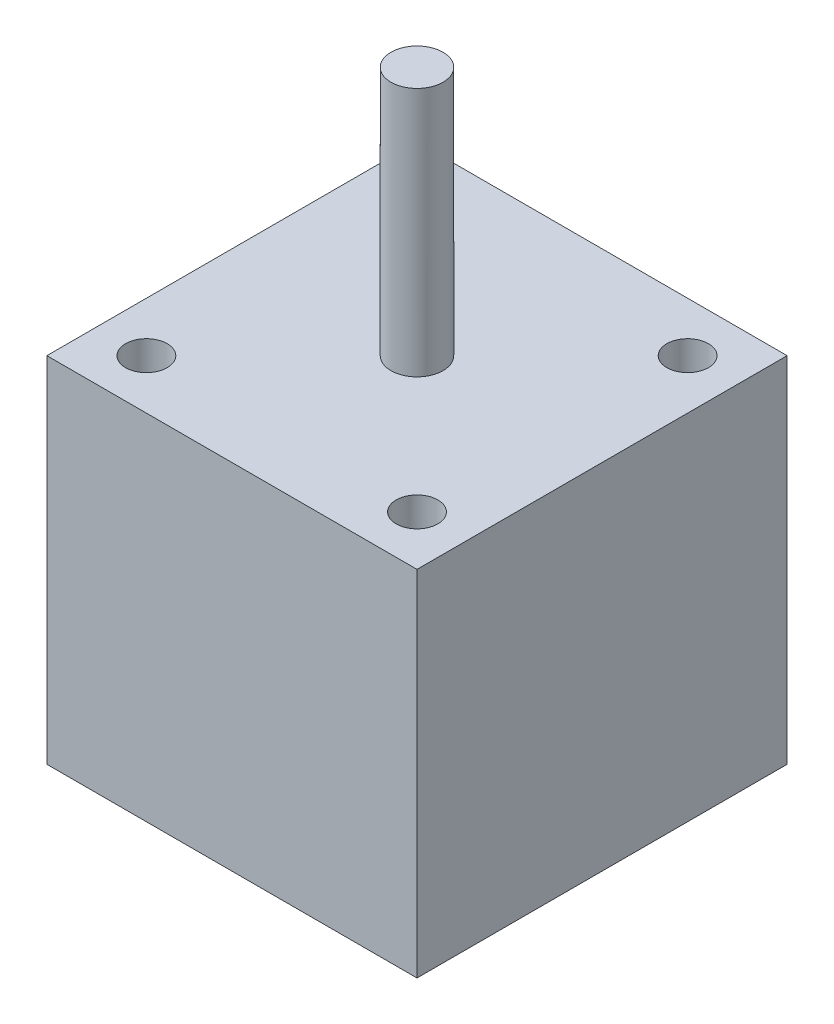
SolidWorks part; units mm, degrees
ref_plane "Front Plane" through (0, 0, 0) normal (0, 0, 1) x (1, 0, 0)
ref_plane "Top Plane" through (0, 0, 0) normal (0, 1, 0) x (1, 0, 0)
ref_plane "Right Plane" through (0, 0, 0) normal (1, 0, 0) x (0, 0, -1)
sketch "Sketch1" plane through (0, 0, 0) normal (0, 1, 0) x (1, 0, 0)
  line L1 (-17.78, -17.78) -> (17.78, -17.78)
  line L2 (-17.78, -17.78) -> (-17.78, 17.78)
  line L3 (-17.78, 17.78) -> (17.78, 17.78)
  line L4 (17.78, -17.78) -> (17.78, 17.78)
  line L5 (-17.78, -17.78) -> (17.78, 17.78) construction
  line L6 (-17.78, 17.78) -> (17.78, -17.78) construction
  point P0 (0, 0)
  dimension "D1" = 35.56
extrude "Boss-Extrude1" add sketch "Sketch1" along normal blind 34
sketch "Sketch2" plane through (0, 34, 0) normal (0, 1, 0) x (1, 0, 0)
  circle A0 centre (0, 0) radius 2.5
  dimension "D1" = 5
extrude "Boss-Extrude2" add sketch "Sketch2" along normal blind 24
sketch "Sketch3" plane through (0, 0, 0) normal (0, -1, 0) x (1, 0, 0)
  circle A0 centre (0, 0) radius 2.5
  dimension "D1" = 5
extrude "Boss-Extrude3" add sketch "Sketch3" along normal blind 12
sketch "Sketch4" plane through (0, 34, 0) normal (0, 1, 0) x (1, 0, 0)
  line L1 (-13, 13) -> (13, 13) construction
  line L2 (-13, 13) -> (-13, -13) construction
  line L3 (-13, -13) -> (13, -13) construction
  line L4 (13, 13) -> (13, -13) construction
  circle A0 centre (-13, 13) radius 2
  circle A1 centre (13, 13) radius 2
  circle A2 centre (13, -13) radius 2
  circle A3 centre (-13, -13) radius 2
  point P4 (0, 13)
  point P6 (-13, 0)
  dimension "D2" = 4
  dimension "D1" = 26
extrude "Cut-Extrude1" cut sketch "Sketch4" against normal up to surface (34 mm away) up to face at (0, 0, -2.5)
